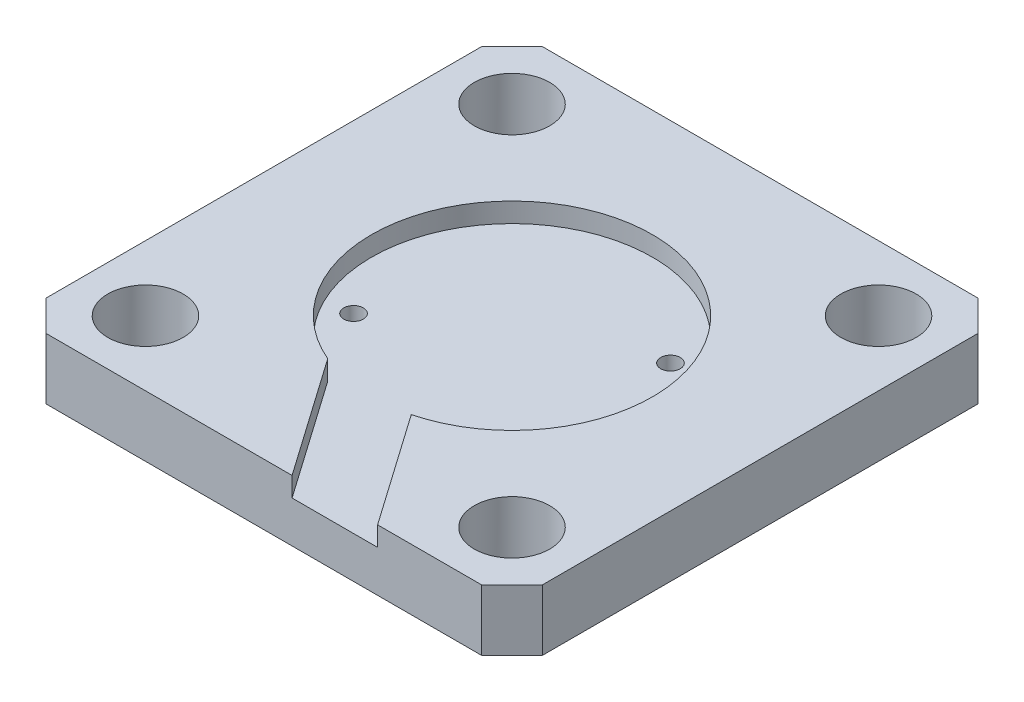
SolidWorks part; units mm, degrees
ref_plane "Front Plane" through (0, 0, 0) normal (0, 0, 1) x (1, 0, 0)
ref_plane "Top Plane" through (0, 0, 0) normal (0, 1, 0) x (1, 0, 0)
ref_plane "Right Plane" through (0, 0, 0) normal (1, 0, 0) x (0, 0, -1)
sketch "Sketch1" plane through (0, 0, 0) normal (0, 1, 0) x (1, 0, 0)
  line L1 (-20.32, -20.32) -> (20.32, -20.32)
  line L2 (-20.32, -20.32) -> (-20.32, 20.32)
  line L3 (-20.32, 20.32) -> (20.32, 20.32)
  line L4 (20.32, -20.32) -> (20.32, 20.32)
  line L5 (-20.32, -20.32) -> (20.32, 20.32) construction
  line L6 (-20.32, 20.32) -> (20.32, -20.32) construction
  point P0 (0, 0)
  dimension "D1" = 40.64
  dimension "D2" = 40.64
extrude "Boss-Extrude1" add sketch "Sketch1" along normal blind 5
sketch "Sketch2" plane through (0, 5, 0) normal (0, 1, 0) x (1, 0, 0)
  line L1 (-15, -15) -> (15, -15) construction
  line L2 (-15, -15) -> (-15, 15) construction
  line L3 (-15, 15) -> (15, 15) construction
  line L4 (15, -15) -> (15, 15) construction
  line L5 (-15, -15) -> (15, 15) construction
  line L6 (-15, 15) -> (15, -15) construction
  circle A0 centre (-15, 15) radius 3.085
  circle A1 centre (15, 15) radius 3.085
  circle A2 centre (15, -15) radius 3.085
  circle A3 centre (-15, -15) radius 3.085
  point P0 (0, 0)
  dimension "D3" = 6.17
  dimension "D1" = 30
  dimension "D2" = 30
  dimension "D4" = 2
  dimension "D5" = 2
extrude "Cut-Extrude1" cut sketch "Sketch2" against normal up to next contours A0 | A1 | A2 | A3
chamfer "Chamfer1" distance 2.5 angle 45 4 edges at (-20.32, 2.5, 20.32) (20.32, 2.5, 20.32) (20.32, 2.5, -20.32) (-20.32, 2.5, -20.32)
sketch "Sketch3" plane through (0, 5, 0) normal (0, 1, 0) x (1, 0, 0)
  circle A0 centre (0, 0) radius 11.5
  dimension "D1" = 23
extrude "Cut-Extrude2" cut sketch "Sketch3" against normal blind 1.6
ref_point "Point1"
sketch "Sketch4" plane through (0, 5, 0) normal (0, 1, 0) x (1, 0, 0)
  circle A0 centre (0, 0) radius 12000
  circle A1 centre (0, 0) radius 15.5
  circle A2 centre (0, 0) radius 11.925
  dimension "D1" = 24000
  dimension "D2" = 31
  dimension "D3" = 23.85
extrude "Cut-Extrude3" [suppressed] cut sketch "Sketch4" against normal blind 2.6 contours A1 A2 | A0
sketch "Sketch5" plane through (0, 3.4, 0) normal (0, 1, 0) x (1, 0, 0)
  line L0 (0, 0) -> (0, -11.5) construction
  line L1 (-1, -9.5) -> (1, -9.5) construction
  line L2 (-1, -11.5) -> (1, -11.5) construction
  line L3 (-1, -11.5) -> (-1, -7.5) construction
  line L4 (-1, -7.5) -> (1, -7.5) construction
  line L5 (1, -11.5) -> (1, -7.5) construction
  line L6 (-1, -11.5) -> (1, -7.5) construction
  line L7 (-1, -7.5) -> (1, -11.5) construction
  line L8 (-1, -7.8) -> (1, -7.8)
  line L9 (-1, -11.2) -> (1, -11.2)
  circle A0 centre (0, 0) radius 11.5 construction
  circle A1 centre (0, 0) radius 9.5 construction
  arc A2 (-1, -7.8) -> (-1, -11.2) centre (-1, -9.5) ccw
  arc A7 (1, -11.2) -> (1, -7.8) centre (1, -9.5) ccw
  point P6 (0, -9.5)
  point P14 (0, -9.5)
  dimension "D1" = 4
  dimension "D2" = 2
  dimension "D3" = 0
  dimension "D4" = 3.4
extrude "Cut-Extrude4" [suppressed] cut sketch "Sketch5" against normal through all contours L9 A7 L8 A2
sketch "Sketch6" plane through (0, 5, 0) normal (0, 1, 0) x (1, 0, 0)
  line L8 (-20.32, 17.82) -> (-20.32, -17.82)
  line L9 (-20.32, 17.82) -> (-20.32, -17.82)
  line L10 (-20.32, -17.82) -> (-17.82, -20.32)
  line L11 (-20.32, -17.82) -> (-17.82, -20.32)
  line L12 (-17.82, -20.32) -> (17.82, -20.32)
  line L13 (-17.82, -20.32) -> (17.82, -20.32)
  line L14 (17.82, -20.32) -> (20.32, -17.82)
  line L15 (17.82, -20.32) -> (20.32, -17.82)
  line L16 (20.32, -17.82) -> (20.32, 17.82)
  line L17 (20.32, -17.82) -> (20.32, 17.82)
  line L18 (20.32, 17.82) -> (17.82, 20.32)
  line L19 (20.32, 17.82) -> (17.82, 20.32)
  line L20 (17.82, 20.32) -> (-17.82, 20.32)
  line L21 (17.82, 20.32) -> (-17.82, 20.32)
  line L22 (-17.82, 20.32) -> (-20.32, 17.82)
  line L23 (-17.82, 20.32) -> (-20.32, 17.82)
  circle A3 centre (0, 0) radius 11.5 construction
  circle A4 centre (0, 0) radius 11.5
  dimension "D1" = 0
extrude "Cut-Extrude5" [suppressed] cut sketch "Sketch6" against normal blind 1
sketch "Sketch7" plane through (0, 3.4, 0) normal (0, 1, 0) x (1, 0, 0)
  line L0 (8.2431, 4.7273) -> (-8.2431, -4.7273) construction
  circle A0 centre (8.2431, 4.7273) radius 0.8
  circle A1 centre (0, 0) radius 11.5
  circle A2 centre (0, 0) radius 11.5 construction
  circle A3 centre (8.2431, 4.7273) radius 1
  circle A4 centre (8.2431, 4.7273) radius 1 construction
  circle A5 centre (-8.2431, -4.7273) radius 1
  circle A6 centre (-8.2431, -4.7273) radius 1 construction
  circle A7 centre (0, 0) radius 11
  circle A8 centre (0, 0) radius 11 construction
  circle A9 centre (-8.2431, -4.7273) radius 0.8
  dimension "D5" = 1.6
  dimension "D6" = 1.6
  dimension "D1" = 0
  dimension "D2" = 0
  dimension "D3" = 0
  dimension "D4" = 0
extrude "Cut-Extrude6" cut sketch "Sketch7" against normal through all contours A9 | A0
sketch "Sketch8" plane through (0, 5, 0) normal (0, 1, 0) x (1, 0, 0)
  line L0 (-5.9882, -8.4546) -> (-1.2912, -5.1657)
  line L1 (2.32, -20.32) -> (9.32, -20.32)
  line L2 (9.32, -20.32) -> (-8.7925, 5.5474)
  line L3 (2.32, -20.32) -> (-14.076, 3.0959)
  line L8 (-20.32, 17.82) -> (-20.32, -17.82)
  line L9 (-20.32, -17.82) -> (-17.82, -20.32)
  line L10 (-17.82, -20.32) -> (17.82, -20.32)
  line L11 (17.82, -20.32) -> (20.32, -17.82)
  line L12 (20.32, -17.82) -> (20.32, 17.82)
  line L13 (20.32, 17.82) -> (17.82, 20.32)
  line L14 (17.82, 20.32) -> (-17.82, 20.32)
  line L15 (-17.82, 20.32) -> (-20.32, 17.82)
  line L16 (-20.32, 17.82) -> (-20.32, -17.82)
  line L17 (-20.32, -17.82) -> (-17.82, -20.32)
  line L18 (-17.82, -20.32) -> (17.82, -20.32)
  line L19 (17.82, -20.32) -> (20.32, -17.82)
  line L20 (20.32, -17.82) -> (20.32, 17.82)
  line L21 (20.32, 17.82) -> (17.82, 20.32)
  line L22 (17.82, 20.32) -> (-17.82, 20.32)
  line L23 (-17.82, 20.32) -> (-20.32, 17.82)
  circle M10 centre (0, 0) radius 11.5
  line M17 (-17.82, -20.32) -> (17.82, -20.32)
  dimension "D2" = 55
  dimension "D3" = 55
  dimension "D4" = 7
  dimension "D5" = 11
  dimension "D6" = 18.5
  dimension "D1" = 0
extrude "Cut-Extrude7" cut sketch "Sketch8" against normal up to surface (1.6 mm away) contours L3 L2 M17 M10 up to face at (-8.2431, 3.4, 5.5273)
fillet "Fillet1" [suppressed] radius 3.125
